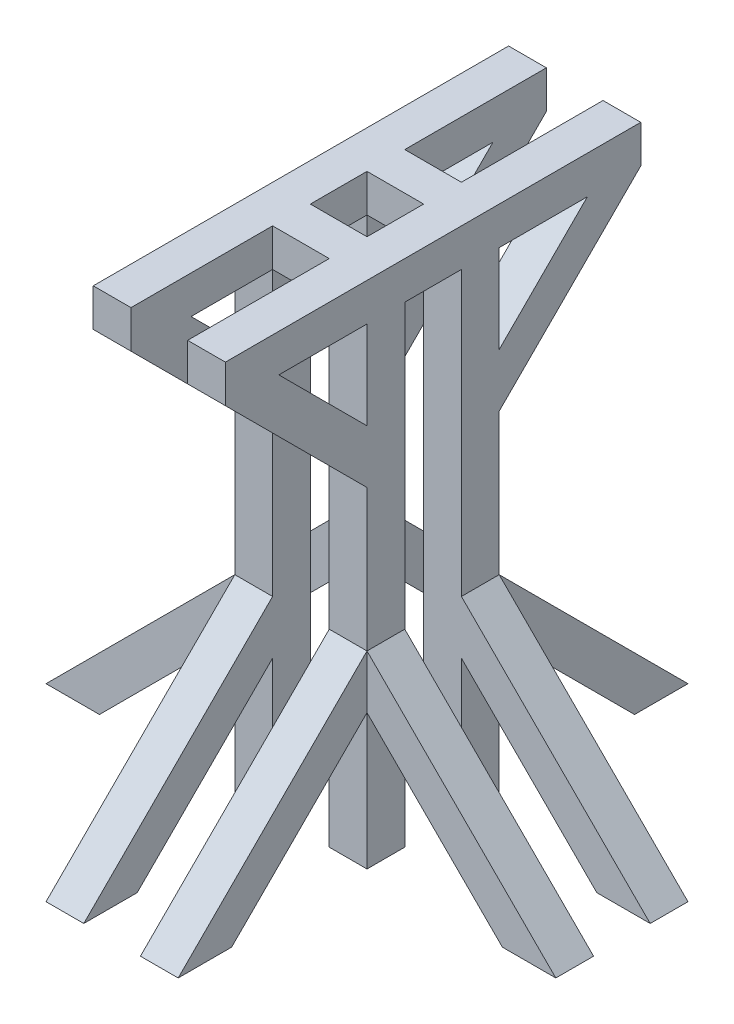
SolidWorks part; units mm, degrees
ref_plane "前视基准面" through (0, 0, 0) normal (0, 0, 1) x (1, 0, 0)
ref_plane "上视基准面" through (0, 0, 0) normal (0, 1, 0) x (1, 0, 0)
ref_plane "右视基准面" through (0, 0, 0) normal (1, 0, 0) x (0, 0, -1)
sketch "草图1" plane through (0, 0, 0) normal (0, 1, 0) x (1, 0, 0)
  line L1 (0, 0) -> (40, 0)
  line L2 (0, 0) -> (0, -40)
  line L3 (0, -40) -> (40, -40)
  line L4 (40, 0) -> (40, -40)
  line L5 (100, 0) -> (140, 0)
  line L6 (100, 0) -> (100, -40)
  line L7 (100, -40) -> (140, -40)
  line L8 (140, 0) -> (140, -40)
  line L9 (0, -140) -> (40, -140)
  line L10 (0, -140) -> (0, -100)
  line L11 (0, -100) -> (40, -100)
  line L12 (40, -140) -> (40, -100)
  line L13 (100, -140) -> (140, -140)
  line L14 (100, -140) -> (100, -100)
  line L15 (100, -100) -> (140, -100)
  line L16 (140, -140) -> (140, -100)
  point P17 (20, 0)
  point P18 (120, 0)
  point P19 (0, -20)
  point P20 (0, -120)
  dimension "D1" = 40
  dimension "D2" = 40
  dimension "D3" = 100
  dimension "D4" = 100
extrude "凸台-拉伸1" add sketch "草图1" along normal blind 500
sketch "草图3" plane through (0, 500, 0) normal (0, 1, 0) x (1, 0, 0)
  line L0 (40, -40) -> (40, 0) construction
  line L1 (40, 150) -> (0, 150)
  line L2 (40, 150) -> (40, -290)
  line L3 (40, -290) -> (0, -290)
  line L4 (0, 150) -> (0, -290)
  line L5 (0, 0) -> (0, -40) construction
  line L6 (0, -140) -> (40, -140) construction
  line L7 (40, 0) -> (0, 0) construction
  dimension "D1" = 150
  dimension "D2" = 150
extrude "凸台-拉伸2" add sketch "草图3" along normal blind 40 contours L2 L3 L4 L1
sketch "草图4" plane through (0, 500, 0) normal (0, 1, 0) x (1, 0, 0)
  line L0 (140, 0) -> (100, 0) construction
  line L1 (140, 150) -> (100, 150)
  line L2 (140, 150) -> (140, -290)
  line L3 (140, -290) -> (100, -290)
  line L4 (100, 150) -> (100, -290)
  line L5 (140, -140) -> (140, -100) construction
  line L6 (100, -100) -> (100, -140) construction
  line L7 (100, -140) -> (140, -140) construction
  dimension "D1" = 150
  dimension "D2" = 150
extrude "凸台-拉伸3" add sketch "草图4" along normal blind 40
sketch "草图5" plane through (40, 0, 0) normal (1, 0, 0) x (0, 0, -1)
  line L0 (150, 540) -> (-290, 540) construction
  line L1 (-140, 500) -> (-100, 500)
  line L2 (-140, 500) -> (-140, 540)
  line L3 (-140, 540) -> (-100, 540)
  line L4 (-100, 500) -> (-100, 540)
  line L6 (0, 500) -> (-40, 500)
  line L7 (0, 500) -> (0, 540)
  line L8 (0, 540) -> (-40, 540)
  line L9 (-40, 500) -> (-40, 540)
  dimension "D1" = 40
  dimension "D2" = 40
extrude "凸台-拉伸4" add sketch "草图5" along normal up to next (100 mm away)
sketch "草图6" plane through (140, 0, 0) normal (1, 0, 0) x (0, 0, -1)
  line L0 (-290, 500) -> (-140, 350)
  line L1 (-140, 500) -> (-140, 0) construction
  line L2 (-233.4315, 500) -> (-140, 406.5685)
  line L3 (-290, 500) -> (-140, 500) construction
  line L4 (150, 500) -> (0, 350)
  line L5 (0, 500) -> (0, 0) construction
  line L6 (93.4315, 500) -> (0, 406.5685)
  line L7 (0, 500) -> (150, 500) construction
  line L8 (-290, 500) -> (-233.4315, 500)
  line L9 (-140, 406.5685) -> (-140, 350)
  line L10 (0, 406.5685) -> (0, 350)
  line L11 (93.4315, 500) -> (150, 500)
  dimension "D1" = 40
  dimension "D2" = 40
  dimension "D3" = 45
  dimension "D4" = 45
extrude "凸台-拉伸5" add sketch "草图6" against normal blind 40
sketch "草图7" plane through (0, 0, 0) normal (-1, 0, 0) x (0, 0, 1)
  line L11 (-150, 500) -> (0, 350)
  line L12 (0, 500) -> (0, 0) construction
  line L13 (290, 500) -> (140, 350)
  line L14 (140, 500) -> (140, 0) construction
  line L15 (-93.4315, 500) -> (0, 406.5685)
  line L16 (-150, 500) -> (0, 500) construction
  line L17 (226.3604, 500) -> (140, 413.6396)
  line L18 (140, 500) -> (290, 500) construction
  line L19 (-150, 500) -> (-93.4315, 500)
  line L20 (0, 406.5685) -> (0, 350)
  line L21 (140, 413.6396) -> (140, 350)
  line L22 (226.3604, 500) -> (290, 500)
  dimension "D1" = 40
  dimension "D2" = 45
  dimension "D3" = 45
  dimension "D4" = 45
extrude "凸台-拉伸6" add sketch "草图7" against normal blind 40
sketch "草图8" plane through (0, 0, 0) normal (-1, 0, 0) x (0, 0, 1)
  line L0 (0, 200) -> (-200, 0)
  line L1 (0, 350) -> (0, 0) construction
  line L2 (0, 143.4315) -> (-143.4315, 0)
  line L3 (140, 200) -> (340, 0)
  line L4 (140, 350) -> (140, 0) construction
  line L5 (140, 143.4315) -> (283.4315, 0)
  line L6 (620.5776, 0) -> (-535.1016, 0)
  line L7 (0, 200) -> (0, 143.4315)
  line L8 (140, 200) -> (140, 143.4315)
  line L9 (283.4315, 0) -> (340, 0)
  line L10 (-200, 0) -> (-143.4315, 0)
  point P15 (0, 0)
  point P16 (0, 0)
  line M17 (140, 0) -> (140, 350)
  line M23 (0, 350) -> (0, 0)
  dimension "D1" = 45
  dimension "D2" = 45
  dimension "D3" = 40
  dimension "D4" = 40
  dimension "D5" = 200
  dimension "D6" = 200
extrude "凸台-拉伸7" add sketch "草图8" against normal blind 40 contours L6 L2 L0 M23 | L6 L3 L5 M17
pattern_linear "阵列(线性)1" count 2 spacing 100 along (1, 0, 0) of "凸台-拉伸7"
sketch "草图9" plane through (0, 0, 0) normal (0, 0, -1) x (-1, 0, 0)
  line L0 (0, 200) -> (200, 0)
  line L1 (-140, 200) -> (-340, 0)
  line L2 (-140, 143.4315) -> (-283.4315, 0)
  line L3 (0, 143.4315) -> (143.4315, 0)
  line L4 (378.9372, 0) -> (-646.7813, 0)
  line L5 (-40, 0) -> (0, 0) construction
  line L6 (-140, 200) -> (-140, 143.4315)
  line L7 (143.4315, 0) -> (200, 0)
  line L8 (0, 200) -> (0, 143.4315)
  line L9 (-340, 0) -> (-283.4315, 0)
  dimension "D1" = 45
  dimension "D2" = 45
  dimension "D3" = 40
  dimension "D4" = 40
extrude "凸台-拉伸8" add sketch "草图9" against normal blind 40 contours L6 L1 L4 L2 | L0 L8 L3 L4
sketch "草图10" plane through (0, 0, 140) normal (0, 0, 1) x (1, 0, 0)
  line L0 (0, 200) -> (-200, 0)
  line L1 (0, 143.4315) -> (-143.4315, 0)
  line L2 (140, 200) -> (340, 0)
  line L3 (140, 143.4315) -> (283.4315, 0)
  line L4 (-255.9052, 0) -> (470.8635, 0)
  line L5 (0, 200) -> (0, 143.4315)
  line L6 (-200, 0) -> (-143.4315, 0)
  line L7 (140, 200) -> (140, 143.4315)
  line L8 (283.4315, 0) -> (340, 0)
  point P19 (240, 100)
  dimension "D1" = 45
  dimension "D2" = 45
  dimension "D3" = 40
  dimension "D4" = 40
extrude "凸台-拉伸9" add sketch "草图10" against normal blind 40 contours L5 L0 L4 L1 | L2 L7 L3 L4
